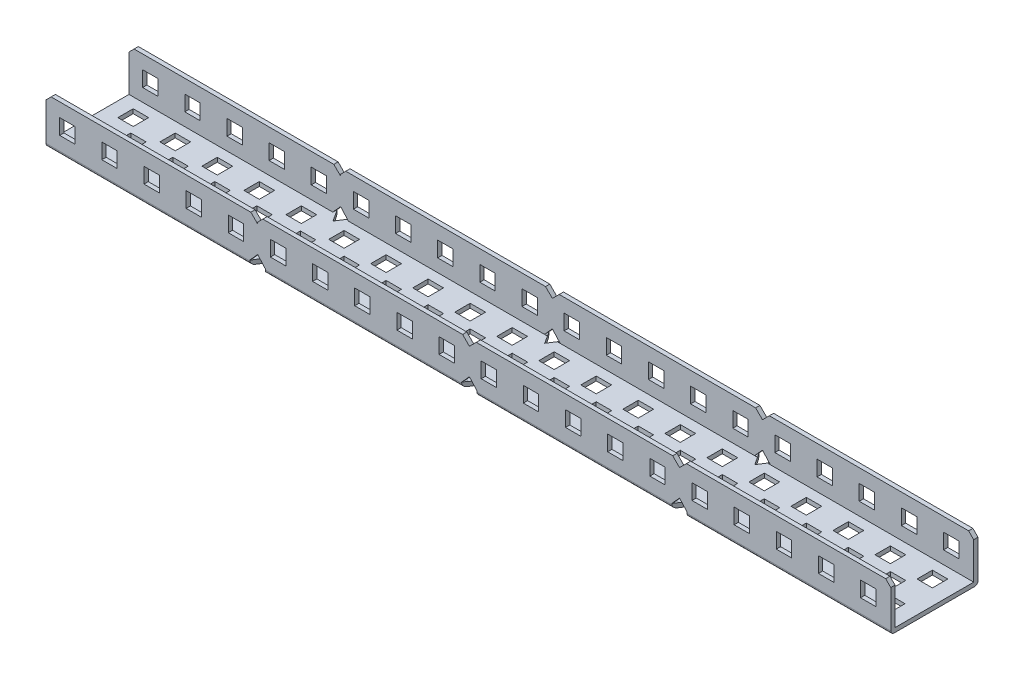
SolidWorks part; units mm, degrees
ref_plane "Front Plane" through (0, 0, 0) normal (0, 0, 1) x (1, 0, 0)
ref_plane "Top Plane" through (0, 0, 0) normal (0, 1, 0) x (1, 0, 0)
ref_plane "Right Plane" through (0, 0, 0) normal (1, 0, 0) x (0, 0, -1)
sketch "Sketch1" plane through (0, 0, 0) normal (0, 1, 0) x (1, 0, 0)
  line L1 (0, 0) -> (191, 0)
  line L2 (0, 0) -> (0, 25.5)
  line L3 (0, 25.5) -> (191, 25.5)
  line L4 (191, 0) -> (191, 25.5)
  dimension "D1" = 25.5
  dimension "D2" = 191
extrude "Boss-Extrude1" add sketch "Sketch1" along normal blind 1.25
sketch "Sketch2" plane through (0, 1.25, 0) normal (0, 1, 0) x (1, 0, 0)
  line L0 (191, 0) -> (191, 25.5) construction
  line L1 (0, 25.5) -> (191, 25.5)
  line L2 (0, 25.5) -> (0, 24.25)
  line L3 (0, 24.25) -> (191, 24.25)
  line L4 (191, 25.5) -> (191, 24.25)
  line L5 (0, 25.5) -> (0, 0) construction
  line L6 (191, 0) -> (0, 0)
  line L7 (191, 0) -> (191, 1.25)
  line L8 (191, 1.25) -> (0, 1.25)
  line L9 (0, 0) -> (0, 1.25)
  dimension "D1" = 1.25
  dimension "D2" = 1.25
extrude "Boss-Extrude2" add sketch "Sketch2" along normal blind 12.25
sketch "Sketch3" plane through (0, 0, 0) normal (0, -1, 0) x (-1, 0, 0)
  line L0 (0, 25.5) -> (0, 0) construction
  line L1 (-4, 4.25) -> (-8.5, 4.25)
  line L2 (-4, 4.25) -> (-4, 8.75)
  line L3 (-4, 8.75) -> (-8.5, 8.75)
  line L4 (-8.5, 4.25) -> (-8.5, 8.75)
  line L5 (-4, 16.75) -> (-8.5, 16.75)
  line L6 (-4, 16.75) -> (-4, 21.25)
  line L7 (-4, 21.25) -> (-8.5, 21.25)
  line L8 (-8.5, 16.75) -> (-8.5, 21.25)
  line L9 (-191, 25.5) -> (0, 25.5) construction
  line L10 (-16.2857, 4.25) -> (-20.7857, 4.25)
  line L11 (-10.5, 10.25) -> (-15, 10.25)
  line L12 (-10.5, 10.25) -> (-10.5, 14.75)
  line L13 (-10.5, 14.75) -> (-15, 14.75)
  line L14 (-15, 10.25) -> (-15, 14.75)
  line L15 (-16.2857, 4.25) -> (-16.2857, 8.75)
  line L16 (-16.2857, 8.75) -> (-20.7857, 8.75)
  line L17 (-20.7857, 4.25) -> (-20.7857, 8.75)
  line L18 (-16.2857, 16.75) -> (-20.7857, 16.75)
  line L19 (-16.2857, 16.75) -> (-16.2857, 21.25)
  line L20 (-16.2857, 21.25) -> (-20.7857, 21.25)
  line L21 (-20.7857, 16.75) -> (-20.7857, 21.25)
  line L22 (-22.7857, 10.25) -> (-27.2857, 10.25)
  line L23 (-22.7857, 10.25) -> (-22.7857, 14.75)
  line L24 (-22.7857, 14.75) -> (-27.2857, 14.75)
  line L25 (-27.2857, 10.25) -> (-27.2857, 14.75)
  line L26 (-28.5714, 4.25) -> (-33.0714, 4.25)
  line L27 (-28.5714, 4.25) -> (-28.5714, 8.75)
  line L28 (-28.5714, 8.75) -> (-33.0714, 8.75)
  line L29 (-33.0714, 4.25) -> (-33.0714, 8.75)
  line L30 (-28.5714, 16.75) -> (-33.0714, 16.75)
  line L31 (-28.5714, 16.75) -> (-28.5714, 21.25)
  line L32 (-28.5714, 21.25) -> (-33.0714, 21.25)
  line L33 (-33.0714, 16.75) -> (-33.0714, 21.25)
  line L34 (-35.0714, 10.25) -> (-39.5714, 10.25)
  line L35 (-35.0714, 10.25) -> (-35.0714, 14.75)
  line L36 (-35.0714, 14.75) -> (-39.5714, 14.75)
  line L37 (-39.5714, 10.25) -> (-39.5714, 14.75)
  line L38 (-40.8571, 4.25) -> (-45.3571, 4.25)
  line L39 (-40.8571, 4.25) -> (-40.8571, 8.75)
  line L40 (-40.8571, 8.75) -> (-45.3571, 8.75)
  line L41 (-45.3571, 4.25) -> (-45.3571, 8.75)
  line L42 (-40.8571, 16.75) -> (-45.3571, 16.75)
  line L43 (-40.8571, 16.75) -> (-40.8571, 21.25)
  line L44 (-40.8571, 21.25) -> (-45.3571, 21.25)
  line L45 (-45.3571, 16.75) -> (-45.3571, 21.25)
  line L46 (-47.3571, 10.25) -> (-51.8571, 10.25)
  line L47 (-47.3571, 10.25) -> (-47.3571, 14.75)
  line L48 (-47.3571, 14.75) -> (-51.8571, 14.75)
  line L49 (-51.8571, 10.25) -> (-51.8571, 14.75)
  line L50 (-53.1429, 4.25) -> (-57.6429, 4.25)
  line L51 (-53.1429, 4.25) -> (-53.1429, 8.75)
  line L52 (-53.1429, 8.75) -> (-57.6429, 8.75)
  line L53 (-57.6429, 4.25) -> (-57.6429, 8.75)
  line L54 (-53.1429, 16.75) -> (-57.6429, 16.75)
  line L55 (-53.1429, 16.75) -> (-53.1429, 21.25)
  line L56 (-53.1429, 21.25) -> (-57.6429, 21.25)
  line L57 (-57.6429, 16.75) -> (-57.6429, 21.25)
  line L58 (-59.6429, 10.25) -> (-64.1429, 10.25)
  line L59 (-59.6429, 10.25) -> (-59.6429, 14.75)
  line L60 (-59.6429, 14.75) -> (-64.1429, 14.75)
  line L61 (-64.1429, 10.25) -> (-64.1429, 14.75)
  line L62 (-65.4286, 4.25) -> (-69.9286, 4.25)
  line L63 (-65.4286, 4.25) -> (-65.4286, 8.75)
  line L64 (-65.4286, 8.75) -> (-69.9286, 8.75)
  line L65 (-69.9286, 4.25) -> (-69.9286, 8.75)
  line L66 (-65.4286, 16.75) -> (-69.9286, 16.75)
  line L67 (-65.4286, 16.75) -> (-65.4286, 21.25)
  line L68 (-65.4286, 21.25) -> (-69.9286, 21.25)
  line L69 (-69.9286, 16.75) -> (-69.9286, 21.25)
  line L70 (-71.9286, 10.25) -> (-76.4286, 10.25)
  line L71 (-71.9286, 10.25) -> (-71.9286, 14.75)
  line L72 (-71.9286, 14.75) -> (-76.4286, 14.75)
  line L73 (-76.4286, 10.25) -> (-76.4286, 14.75)
  line L74 (-77.7143, 4.25) -> (-82.2143, 4.25)
  line L75 (-77.7143, 4.25) -> (-77.7143, 8.75)
  line L76 (-77.7143, 8.75) -> (-82.2143, 8.75)
  line L77 (-82.2143, 4.25) -> (-82.2143, 8.75)
  line L78 (-77.7143, 16.75) -> (-82.2143, 16.75)
  line L79 (-77.7143, 16.75) -> (-77.7143, 21.25)
  line L80 (-77.7143, 21.25) -> (-82.2143, 21.25)
  line L81 (-82.2143, 16.75) -> (-82.2143, 21.25)
  line L82 (-84.2143, 10.25) -> (-88.7143, 10.25)
  line L83 (-84.2143, 10.25) -> (-84.2143, 14.75)
  line L84 (-84.2143, 14.75) -> (-88.7143, 14.75)
  line L85 (-88.7143, 10.25) -> (-88.7143, 14.75)
  line L86 (-90, 4.25) -> (-94.5, 4.25)
  line L87 (-90, 4.25) -> (-90, 8.75)
  line L88 (-90, 8.75) -> (-94.5, 8.75)
  line L89 (-94.5, 4.25) -> (-94.5, 8.75)
  line L90 (-90, 16.75) -> (-94.5, 16.75)
  line L91 (-90, 16.75) -> (-90, 21.25)
  line L92 (-90, 21.25) -> (-94.5, 21.25)
  line L93 (-94.5, 16.75) -> (-94.5, 21.25)
  line L94 (-96.5, 10.25) -> (-101, 10.25)
  line L95 (-96.5, 10.25) -> (-96.5, 14.75)
  line L96 (-96.5, 14.75) -> (-101, 14.75)
  line L97 (-101, 10.25) -> (-101, 14.75)
  line L98 (-102.2857, 4.25) -> (-106.7857, 4.25)
  line L99 (-102.2857, 4.25) -> (-102.2857, 8.75)
  line L100 (-102.2857, 8.75) -> (-106.7857, 8.75)
  line L101 (-106.7857, 4.25) -> (-106.7857, 8.75)
  line L102 (-102.2857, 16.75) -> (-106.7857, 16.75)
  line L103 (-102.2857, 16.75) -> (-102.2857, 21.25)
  line L104 (-102.2857, 21.25) -> (-106.7857, 21.25)
  line L105 (-106.7857, 16.75) -> (-106.7857, 21.25)
  line L106 (-108.7857, 10.25) -> (-113.2857, 10.25)
  line L107 (-108.7857, 10.25) -> (-108.7857, 14.75)
  line L108 (-108.7857, 14.75) -> (-113.2857, 14.75)
  line L109 (-113.2857, 10.25) -> (-113.2857, 14.75)
  line L110 (-114.5714, 4.25) -> (-119.0714, 4.25)
  line L111 (-114.5714, 4.25) -> (-114.5714, 8.75)
  line L112 (-114.5714, 8.75) -> (-119.0714, 8.75)
  line L113 (-119.0714, 4.25) -> (-119.0714, 8.75)
  line L114 (-114.5714, 16.75) -> (-119.0714, 16.75)
  line L115 (-114.5714, 16.75) -> (-114.5714, 21.25)
  line L116 (-114.5714, 21.25) -> (-119.0714, 21.25)
  line L117 (-119.0714, 16.75) -> (-119.0714, 21.25)
  line L118 (-121.0714, 10.25) -> (-125.5714, 10.25)
  line L119 (-121.0714, 10.25) -> (-121.0714, 14.75)
  line L120 (-121.0714, 14.75) -> (-125.5714, 14.75)
  line L121 (-125.5714, 10.25) -> (-125.5714, 14.75)
  line L122 (-126.8571, 4.25) -> (-131.3571, 4.25)
  line L123 (-126.8571, 4.25) -> (-126.8571, 8.75)
  line L124 (-126.8571, 8.75) -> (-131.3571, 8.75)
  line L125 (-131.3571, 4.25) -> (-131.3571, 8.75)
  line L126 (-126.8571, 16.75) -> (-131.3571, 16.75)
  line L127 (-126.8571, 16.75) -> (-126.8571, 21.25)
  line L128 (-126.8571, 21.25) -> (-131.3571, 21.25)
  line L129 (-131.3571, 16.75) -> (-131.3571, 21.25)
  line L130 (-133.3571, 10.25) -> (-137.8571, 10.25)
  line L131 (-133.3571, 10.25) -> (-133.3571, 14.75)
  line L132 (-133.3571, 14.75) -> (-137.8571, 14.75)
  line L133 (-137.8571, 10.25) -> (-137.8571, 14.75)
  line L134 (-139.1429, 4.25) -> (-143.6429, 4.25)
  line L135 (-139.1429, 4.25) -> (-139.1429, 8.75)
  line L136 (-139.1429, 8.75) -> (-143.6429, 8.75)
  line L137 (-143.6429, 4.25) -> (-143.6429, 8.75)
  line L138 (-139.1429, 16.75) -> (-143.6429, 16.75)
  line L139 (-139.1429, 16.75) -> (-139.1429, 21.25)
  line L140 (-139.1429, 21.25) -> (-143.6429, 21.25)
  line L141 (-143.6429, 16.75) -> (-143.6429, 21.25)
  line L142 (-145.6429, 10.25) -> (-150.1429, 10.25)
  line L143 (-145.6429, 10.25) -> (-145.6429, 14.75)
  line L144 (-145.6429, 14.75) -> (-150.1429, 14.75)
  line L145 (-150.1429, 10.25) -> (-150.1429, 14.75)
  line L146 (-151.4286, 4.25) -> (-155.9286, 4.25)
  line L147 (-151.4286, 4.25) -> (-151.4286, 8.75)
  line L148 (-151.4286, 8.75) -> (-155.9286, 8.75)
  line L149 (-155.9286, 4.25) -> (-155.9286, 8.75)
  line L150 (-151.4286, 16.75) -> (-155.9286, 16.75)
  line L151 (-151.4286, 16.75) -> (-151.4286, 21.25)
  line L152 (-151.4286, 21.25) -> (-155.9286, 21.25)
  line L153 (-155.9286, 16.75) -> (-155.9286, 21.25)
  line L154 (-157.9286, 10.25) -> (-162.4286, 10.25)
  line L155 (-157.9286, 10.25) -> (-157.9286, 14.75)
  line L156 (-157.9286, 14.75) -> (-162.4286, 14.75)
  line L157 (-162.4286, 10.25) -> (-162.4286, 14.75)
  line L158 (-163.7143, 4.25) -> (-168.2143, 4.25)
  line L159 (-163.7143, 4.25) -> (-163.7143, 8.75)
  line L160 (-163.7143, 8.75) -> (-168.2143, 8.75)
  line L161 (-168.2143, 4.25) -> (-168.2143, 8.75)
  line L162 (-163.7143, 16.75) -> (-168.2143, 16.75)
  line L163 (-163.7143, 16.75) -> (-163.7143, 21.25)
  line L164 (-163.7143, 21.25) -> (-168.2143, 21.25)
  line L165 (-168.2143, 16.75) -> (-168.2143, 21.25)
  line L166 (-170.2143, 10.25) -> (-174.7143, 10.25)
  line L167 (-170.2143, 10.25) -> (-170.2143, 14.75)
  line L168 (-170.2143, 14.75) -> (-174.7143, 14.75)
  line L169 (-174.7143, 10.25) -> (-174.7143, 14.75)
  line L170 (-176, 4.25) -> (-180.5, 4.25)
  line L171 (-176, 4.25) -> (-176, 8.75)
  line L172 (-176, 8.75) -> (-180.5, 8.75)
  line L173 (-180.5, 4.25) -> (-180.5, 8.75)
  line L174 (-176, 16.75) -> (-180.5, 16.75)
  line L175 (-176, 16.75) -> (-176, 21.25)
  line L176 (-176, 21.25) -> (-180.5, 21.25)
  line L177 (-180.5, 16.75) -> (-180.5, 21.25)
  line L178 (-182.5, 10.25) -> (-187, 10.25)
  line L179 (-182.5, 10.25) -> (-182.5, 14.75)
  line L180 (-182.5, 14.75) -> (-187, 14.75)
  line L181 (-187, 10.25) -> (-187, 14.75)
  line L182 (-191, 0) -> (-191, 25.5) construction
  dimension "D1" = 4.5
  dimension "D2" = 4
  dimension "D3" = 8
  dimension "D4" = 4.25
  dimension "D5" = 2
  dimension "D6" = 2
  dimension "D8" = 4
  dimension "D7" = 15
extrude "Cut-Extrude1" cut sketch "Sketch3" against normal blind 12.25
sketch "Sketch4" plane through (0, 0, 0) normal (0, -1, 0) x (1, 0, 0)
  line L0 (61.8929, -3.5) -> (59.6429, 0)
  line L1 (0, 0) -> (191, 0) construction
  line L2 (61.8929, -3.5) -> (64.1429, 0)
  line L3 (59.6429, 0) -> (64.1429, 0)
  line L4 (64.1429, -10.25) -> (59.6429, -10.25) construction
  line L6 (123.3214, -3.5) -> (121.0714, 0)
  line L7 (121.0714, 0) -> (125.5714, 0)
  line L8 (123.3214, -3.5) -> (125.5714, 0)
  line L9 (125.5714, -10.25) -> (121.0714, -10.25) construction
  line L10 (0, -12.75) -> (219.3109, -12.75) construction
  line L12 (121.0714, -25.5) -> (125.5714, -25.5)
  line L13 (123.3214, -22) -> (125.5714, -25.5)
  line L14 (123.3214, -22) -> (121.0714, -25.5)
  line L15 (59.6429, -25.5) -> (64.1429, -25.5)
  line L16 (61.8929, -22) -> (59.6429, -25.5)
  line L17 (61.8929, -22) -> (64.1429, -25.5)
  line L18 (4, -16.75) -> (4, -21.25) construction
  line L19 (47.3571, -14.75) -> (51.8571, -14.75) construction
  point P0 (61.8929, 0)
  point P8 (61.8929, -10.25)
  point P15 (123.3214, -10.25)
  dimension "D1" = 4.5
  dimension "D2" = 3.5
  dimension "D3" = 2
  dimension "D4" = 47.8571
  dimension "D5" = 2
  dimension "D6" = 7.25
extrude "Cut-Extrude2" cut sketch "Sketch4" against normal blind 1.3
sketch "Sketch6" plane through (0, 0, -25.5) normal (0, 0, -1) x (-1, 0, 0)
  line L0 (-125.5714, 1.3) -> (-123.3214, 3.8)
  line L1 (-123.3214, 3.8) -> (-121.0714, 1.3)
  line L2 (-125.5714, 0) -> (-121.0714, 0)
  line L3 (-125.5714, 1.3) -> (-121.0714, 1.3)
  line L4 (-64.1429, 1.3) -> (-61.8929, 3.8)
  line L5 (-61.8929, 3.8) -> (-59.6429, 1.3)
  line L6 (-64.1429, 1.3) -> (-59.6429, 1.3)
  line L8 (-125.3214, 13.5) -> (-121.3214, 13.5)
  line L9 (-125.3214, 13.5) -> (-123.3214, 11.5)
  line L10 (-191, 13.5) -> (0, 13.5) construction
  line L11 (-123.3214, 11.5) -> (-121.3214, 13.5)
  line L12 (-63.8929, 13.5) -> (-61.8929, 11.5)
  line L13 (-61.8929, 11.5) -> (-59.8929, 13.5)
  line L14 (-63.8929, 13.5) -> (-59.8929, 13.5)
  point P29 (-123.3214, 13.5)
  point P31 (-61.8929, 13.5)
  line M2 (-125.5714, 1.3) -> (-121.0714, 1.3)
  line M6 (-64.1429, 1.3) -> (-59.6429, 1.3)
  dimension "D1" = 2.5
  dimension "D3" = 4
  dimension "D4" = 4
  dimension "D5" = 2
  dimension "D2" = 2
extrude "Cut-Extrude4" cut sketch "Sketch6" against normal blind 48.3 contours L1 L0 M2 | L5 L4 M6 | L8 L11 L9 | L14 L13 L12
sketch "Sketch7" plane through (0, 0, -25.5) normal (0, 0, -1) x (-1, 0, 0)
  line L0 (-191, 13.5) -> (-191, 12)
  line L1 (-191, 13.5) -> (-191, 0) construction
  line L2 (-191, 12) -> (-189.5, 13.5)
  line L3 (-191, 13.5) -> (-125.3214, 13.5) construction
  line L4 (-189.5, 13.5) -> (-191, 13.5)
  line L5 (-1.5, 13.5) -> (0, 13.5)
  line L6 (-59.8929, 13.5) -> (0, 13.5) construction
  line L7 (0, 13.5) -> (0, 12)
  line L8 (0, 13.5) -> (0, 0) construction
  line L9 (0, 12) -> (-1.5, 13.5)
  dimension "D1" = 1.5
  dimension "D2" = 1.5
  dimension "D3" = 1.5
  dimension "D4" = 1.5
extrude "Cut-Extrude5" cut sketch "Sketch7" against normal blind 48.3
fillet "Fillet1" radius 1 6 edges at (158.2857, 0, 0) (92.6071, 0, 0) (29.8214, 0, 0) (29.8214, 0, -25.5) (92.6071, 0, -25.5) (158.2857, 0, -25.5)
sketch "Sketch8" plane through (0, 0, 0) normal (0, -1, 0) x (1, 0, 0)
  line L0 (61.8929, -22) -> (59.6429, -25.5)
  line L1 (61.8929, -25.5) -> (0, -25.5)
  line L2 (61.8929, -25.5) -> (61.8929, 0)
  line L3 (61.8929, 0) -> (0, 0)
  line L4 (0, -25.5) -> (0, 0)
  line L5 (57.6429, -21.25) -> (53.1429, -21.25)
  line L6 (57.6429, -21.25) -> (57.6429, -16.75)
  line L7 (57.6429, -16.75) -> (53.1429, -16.75)
  line L8 (53.1429, -21.25) -> (53.1429, -16.75)
  line L9 (51.8571, -14.75) -> (47.3571, -14.75)
  line L10 (51.8571, -14.75) -> (51.8571, -10.25)
  line L11 (51.8571, -10.25) -> (47.3571, -10.25)
  line L12 (47.3571, -14.75) -> (47.3571, -10.25)
  line L13 (45.3571, -21.25) -> (40.8571, -21.25)
  line L14 (45.3571, -21.25) -> (45.3571, -16.75)
  line L15 (45.3571, -16.75) -> (40.8571, -16.75)
  line L16 (40.8571, -21.25) -> (40.8571, -16.75)
  line L17 (45.3571, -8.75) -> (40.8571, -8.75)
  line L18 (45.3571, -8.75) -> (45.3571, -4.25)
  line L19 (45.3571, -4.25) -> (40.8571, -4.25)
  line L20 (40.8571, -8.75) -> (40.8571, -4.25)
  line L21 (57.6429, -8.75) -> (53.1429, -8.75)
  line L22 (57.6429, -8.75) -> (57.6429, -4.25)
  line L23 (57.6429, -4.25) -> (53.1429, -4.25)
  line L24 (53.1429, -8.75) -> (53.1429, -4.25)
  line L25 (39.5714, -14.75) -> (35.0714, -14.75)
  line L26 (39.5714, -14.75) -> (39.5714, -10.25)
  line L27 (39.5714, -10.25) -> (35.0714, -10.25)
  line L28 (35.0714, -14.75) -> (35.0714, -10.25)
  line L29 (33.0714, -21.25) -> (28.5714, -21.25)
  line L30 (33.0714, -21.25) -> (33.0714, -16.75)
  line L31 (33.0714, -16.75) -> (28.5714, -16.75)
  line L32 (28.5714, -21.25) -> (28.5714, -16.75)
  line L33 (33.0714, -8.75) -> (28.5714, -8.75)
  line L34 (33.0714, -8.75) -> (33.0714, -4.25)
  line L35 (33.0714, -4.25) -> (28.5714, -4.25)
  line L36 (28.5714, -8.75) -> (28.5714, -4.25)
  line L37 (27.2857, -14.75) -> (22.7857, -14.75)
  line L38 (27.2857, -14.75) -> (27.2857, -10.25)
  line L39 (27.2857, -10.25) -> (22.7857, -10.25)
  line L40 (22.7857, -14.75) -> (22.7857, -10.25)
  line L41 (20.7857, -21.25) -> (16.2857, -21.25)
  line L42 (20.7857, -21.25) -> (20.7857, -16.75)
  line L43 (20.7857, -16.75) -> (16.2857, -16.75)
  line L44 (16.2857, -21.25) -> (16.2857, -16.75)
  line L45 (20.7857, -8.75) -> (16.2857, -8.75)
  line L46 (20.7857, -8.75) -> (20.7857, -4.25)
  line L47 (20.7857, -4.25) -> (16.2857, -4.25)
  line L48 (16.2857, -8.75) -> (16.2857, -4.25)
  line L49 (15, -14.75) -> (10.5, -14.75)
  line L50 (15, -14.75) -> (15, -10.25)
  line L51 (15, -10.25) -> (10.5, -10.25)
  line L52 (10.5, -14.75) -> (10.5, -10.25)
  line L53 (8.5, -21.25) -> (4, -21.25)
  line L54 (8.5, -21.25) -> (8.5, -16.75)
  line L55 (8.5, -16.75) -> (4, -16.75)
  line L56 (4, -21.25) -> (4, -16.75)
  line L57 (8.5, -8.75) -> (4, -8.75)
  line L58 (8.5, -8.75) -> (8.5, -4.25)
  line L59 (8.5, -4.25) -> (4, -4.25)
  line L60 (4, -8.75) -> (4, -4.25)
  line L61 (59.6429, -25.5) -> (61.8929, -25.5)
  line L62 (61.8929, -3.5) -> (59.6429, 0)
  line L63 (59.6429, 0) -> (61.8929, 0)
  line L64 (0, -22) -> (-2.25, -25.5)
  line L65 (0, -25.5) -> (-61.8929, -25.5)
  line L66 (0, -25.5) -> (0, 0)
  line L67 (0, 0) -> (-61.8929, 0)
  line L68 (-61.8929, -25.5) -> (-61.8929, 0)
  line L69 (-4.25, -21.25) -> (-8.75, -21.25)
  line L70 (-4.25, -21.25) -> (-4.25, -16.75)
  line L71 (-4.25, -16.75) -> (-8.75, -16.75)
  line L72 (-8.75, -21.25) -> (-8.75, -16.75)
  line L73 (-10.0357, -14.75) -> (-14.5357, -14.75)
  line L74 (-10.0357, -14.75) -> (-10.0357, -10.25)
  line L75 (-10.0357, -10.25) -> (-14.5357, -10.25)
  line L76 (-14.5357, -14.75) -> (-14.5357, -10.25)
  line L77 (-16.5357, -21.25) -> (-21.0357, -21.25)
  line L78 (-16.5357, -21.25) -> (-16.5357, -16.75)
  line L79 (-16.5357, -16.75) -> (-21.0357, -16.75)
  line L80 (-21.0357, -21.25) -> (-21.0357, -16.75)
  line L81 (-16.5357, -8.75) -> (-21.0357, -8.75)
  line L82 (-16.5357, -8.75) -> (-16.5357, -4.25)
  line L83 (-16.5357, -4.25) -> (-21.0357, -4.25)
  line L84 (-21.0357, -8.75) -> (-21.0357, -4.25)
  line L85 (-4.25, -8.75) -> (-8.75, -8.75)
  line L86 (-4.25, -8.75) -> (-4.25, -4.25)
  line L87 (-4.25, -4.25) -> (-8.75, -4.25)
  line L88 (-8.75, -8.75) -> (-8.75, -4.25)
  line L89 (-22.3214, -14.75) -> (-26.8214, -14.75)
  line L90 (-22.3214, -14.75) -> (-22.3214, -10.25)
  line L91 (-22.3214, -10.25) -> (-26.8214, -10.25)
  line L92 (-26.8214, -14.75) -> (-26.8214, -10.25)
  line L93 (-28.8214, -21.25) -> (-33.3214, -21.25)
  line L94 (-28.8214, -21.25) -> (-28.8214, -16.75)
  line L95 (-28.8214, -16.75) -> (-33.3214, -16.75)
  line L96 (-33.3214, -21.25) -> (-33.3214, -16.75)
  line L97 (-28.8214, -8.75) -> (-33.3214, -8.75)
  line L98 (-28.8214, -8.75) -> (-28.8214, -4.25)
  line L99 (-28.8214, -4.25) -> (-33.3214, -4.25)
  line L100 (-33.3214, -8.75) -> (-33.3214, -4.25)
  line L101 (-34.6071, -14.75) -> (-39.1071, -14.75)
  line L102 (-34.6071, -14.75) -> (-34.6071, -10.25)
  line L103 (-34.6071, -10.25) -> (-39.1071, -10.25)
  line L104 (-39.1071, -14.75) -> (-39.1071, -10.25)
  line L105 (-41.1071, -21.25) -> (-45.6071, -21.25)
  line L106 (-41.1071, -21.25) -> (-41.1071, -16.75)
  line L107 (-41.1071, -16.75) -> (-45.6071, -16.75)
  line L108 (-45.6071, -21.25) -> (-45.6071, -16.75)
  line L109 (-41.1071, -8.75) -> (-45.6071, -8.75)
  line L110 (-41.1071, -8.75) -> (-41.1071, -4.25)
  line L111 (-41.1071, -4.25) -> (-45.6071, -4.25)
  line L112 (-45.6071, -8.75) -> (-45.6071, -4.25)
  line L113 (-46.8929, -14.75) -> (-51.3929, -14.75)
  line L114 (-46.8929, -14.75) -> (-46.8929, -10.25)
  line L115 (-46.8929, -10.25) -> (-51.3929, -10.25)
  line L116 (-51.3929, -14.75) -> (-51.3929, -10.25)
  line L117 (-53.3929, -21.25) -> (-57.8929, -21.25)
  line L118 (-53.3929, -21.25) -> (-53.3929, -16.75)
  line L119 (-53.3929, -16.75) -> (-57.8929, -16.75)
  line L120 (-57.8929, -21.25) -> (-57.8929, -16.75)
  line L121 (-53.3929, -8.75) -> (-57.8929, -8.75)
  line L122 (-53.3929, -8.75) -> (-53.3929, -4.25)
  line L123 (-53.3929, -4.25) -> (-57.8929, -4.25)
  line L124 (-57.8929, -8.75) -> (-57.8929, -4.25)
  line L125 (-2.25, -25.5) -> (0, -25.5)
  line L126 (0, -3.5) -> (-2.25, 0)
  line L127 (-2.25, 0) -> (0, 0)
  line L128 (0, -3.5) -> (2.25, 0)
  line L129 (2.25, -14.75) -> (-2.25, -14.75)
  line L130 (2.25, -14.75) -> (2.25, -10.25)
  line L131 (2.25, -10.25) -> (-2.25, -10.25)
  line L132 (-2.25, -14.75) -> (-2.25, -10.25)
  line L133 (0, -22) -> (2.25, -25.5)
  point P175 (0, -10.25)
  dimension "D2" = 4.5
  dimension "D1" = 2
extrude "Boss-Extrude3" add sketch "Sketch8" against normal blind 1.25 contours L129 L132 L131 L4 L126 L67 L68 L65 L64 L69 L72 L71 L70 L73 L76 L75 L74 L77 L80 L79 L78 L81 L84 L83 L82 L85 L88 L87 L86 L89 L92 L91 L90 L93 L96 L95 L94 L97 L100 L99 L98
sketch "Sketch9" plane through (0, 0, 0) normal (0, -1, 0) x (1, 0, 0)
  line L0 (0, -22) -> (-2.25, -25.5)
  line L1 (-2.25, -25.5) -> (2.25, -25.5)
  line L2 (0, -25.5) -> (0, -22)
  line L3 (-2.25, 0) -> (0, -3.5)
  line L4 (0, -3.5) -> (0, 0)
  line L5 (2.25, 0) -> (-2.25, 0)
  line L6 (0, -22) -> (2.25, -25.5)
  line L7 (2.25, 0) -> (0, -3.5)
  line L8 (2.25, -10.25) -> (-2.25, -10.25)
  line L9 (-2.25, -10.25) -> (-2.25, -14.75)
  line L10 (-2.25, -14.75) -> (2.25, -14.75)
  line L11 (0, -14.75) -> (0, -10.25)
  line L12 (2.25, -10.25) -> (2.25, -14.75)
extrude "Cut-Extrude6" cut sketch "Sketch9" against normal blind 1.25 contours L12 L8 L11 L10 | L6 L2 L1 | L3 L5 L7
sketch "Sketch10" plane through (0, 0, 0) normal (0, 0, 1) x (1, 0, 0)
  line L0 (1.5, 13.5) -> (0, 12)
  line L1 (0, 12) -> (0, 1.25)
  line L2 (1.5, 13.5) -> (59.8929, 13.5)
  line L3 (59.8929, 13.5) -> (61.8929, 11.5)
  line L4 (61.8929, 11.5) -> (61.8929, 3.8)
  line L5 (61.8929, 3.8) -> (59.6429, 1.3)
  line L6 (59.6429, 1.3) -> (59.6429, 1)
  line L7 (0, 1.25) -> (0, 0)
  line L8 (0, 0) -> (61.8929, 0)
  line L9 (61.8929, 0) -> (61.8929, 3.8)
  line L10 (30.6964, 13.5) -> (30.6964, -8.0722) construction
  line L11 (0, 1.25) -> (2.25, 1.25)
  line L12 (-60.3929, 13.5) -> (-61.8929, 12)
  line L13 (-61.8929, 12) -> (-61.8929, 1.25)
  line L14 (-60.3929, 13.5) -> (-2, 13.5)
  line L15 (-2, 13.5) -> (0, 11.5)
  line L16 (0, 11.5) -> (0, 3.8)
  line L17 (0, 3.8) -> (-2.25, 1.3)
  line L18 (0, 3.8) -> (2.25, 1.25)
  line L19 (-61.8929, 1.25) -> (-61.8929, 0)
  line L20 (-61.8929, 0) -> (0, 0)
  line L21 (0, 0) -> (0, 3.8)
  line L22 (-61.8929, 1.25) -> (-59.6429, 1.25)
  line L23 (-31.1964, 13.5) -> (-31.1964, -8.0722) construction
  line L24 (0, 11.5) -> (2, 13.5)
  line L25 (2, 13.5) -> (-2, 13.5)
  line L26 (-2.25, 1.3) -> (-2.25, 0)
  line L28 (-2.25, 1.3) -> (-2.25, 1) [skipped]
  spline S0 degree 2 poles (59.6429, 1) (59.6889, 0.0907) (60.2857, 0) knots 0 0 0 1 1 1
  dimension "D2" = 4
  dimension "D1" = 2
extrude "Boss-Extrude4" add sketch "Sketch10" against normal blind 25.5
sketch "Sketch11" plane through (191, 0, 0) normal (1, 0, 0) x (0, 0, -1)
  line L0 (1.25, 13.5) -> (1.25, 1.25)
  line L1 (1.25, 1.25) -> (24.25, 1.25)
  line L2 (24.25, 1.25) -> (24.25, 13.5)
  line L3 (24.25, 13.5) -> (1.25, 13.5)
extrude "Cut-Extrude7" cut sketch "Sketch11" against normal blind 284.5
sketch "Sketch12" plane through (0, 0, 0) normal (0, -1, 0) x (1, 0, 0)
  line L0 (0, 0) -> (0, -30.8239) construction
  line L1 (57.6429, -4.25) -> (53.1429, -4.25)
  line L2 (57.6429, -4.25) -> (57.6429, -8.75)
  line L3 (57.6429, -8.75) -> (53.1429, -8.75)
  line L4 (53.1429, -4.25) -> (53.1429, -8.75)
  line L5 (51.8571, -10.25) -> (47.3571, -10.25)
  line L6 (51.8571, -10.25) -> (51.8571, -14.75)
  line L7 (51.8571, -14.75) -> (47.3571, -14.75)
  line L8 (47.3571, -10.25) -> (47.3571, -14.75)
  line L9 (45.3571, -16.75) -> (40.8571, -16.75)
  line L10 (45.3571, -16.75) -> (45.3571, -21.25)
  line L11 (45.3571, -21.25) -> (40.8571, -21.25)
  line L12 (40.8571, -16.75) -> (40.8571, -21.25)
  line L13 (53.1429, -16.75) -> (57.6429, -16.75)
  line L14 (53.1429, -16.75) -> (53.1429, -21.25)
  line L15 (53.1429, -21.25) -> (57.6429, -21.25)
  line L16 (57.6429, -16.75) -> (57.6429, -21.25)
  line L17 (45.3571, -4.25) -> (40.8571, -4.25)
  line L18 (45.3571, -4.25) -> (45.3571, -8.75)
  line L19 (45.3571, -8.75) -> (40.8571, -8.75)
  line L20 (40.8571, -4.25) -> (40.8571, -8.75)
  line L21 (39.5714, -10.25) -> (35.0714, -10.25)
  line L22 (39.5714, -10.25) -> (39.5714, -14.75)
  line L23 (39.5714, -14.75) -> (35.0714, -14.75)
  line L24 (35.0714, -10.25) -> (35.0714, -14.75)
  line L25 (33.0714, -4.25) -> (28.5714, -4.25)
  line L26 (33.0714, -4.25) -> (33.0714, -8.75)
  line L27 (33.0714, -8.75) -> (28.5714, -8.75)
  line L28 (28.5714, -4.25) -> (28.5714, -8.75)
  line L29 (33.0714, -16.75) -> (28.5714, -16.75)
  line L30 (33.0714, -16.75) -> (33.0714, -21.25)
  line L31 (33.0714, -21.25) -> (28.5714, -21.25)
  line L32 (28.5714, -16.75) -> (28.5714, -21.25)
  line L33 (27.2857, -10.25) -> (22.7857, -10.25)
  line L34 (27.2857, -10.25) -> (27.2857, -14.75)
  line L35 (27.2857, -14.75) -> (22.7857, -14.75)
  line L36 (22.7857, -10.25) -> (22.7857, -14.75)
  line L37 (20.7857, -4.25) -> (16.2857, -4.25)
  line L38 (20.7857, -4.25) -> (20.7857, -8.75)
  line L39 (20.7857, -8.75) -> (16.2857, -8.75)
  line L40 (16.2857, -4.25) -> (16.2857, -8.75)
  line L41 (20.7857, -16.75) -> (16.2857, -16.75)
  line L42 (20.7857, -16.75) -> (20.7857, -21.25)
  line L43 (20.7857, -21.25) -> (16.2857, -21.25)
  line L44 (16.2857, -16.75) -> (16.2857, -21.25)
  line L45 (15, -10.25) -> (10.5, -10.25)
  line L46 (15, -10.25) -> (15, -14.75)
  line L47 (15, -14.75) -> (10.5, -14.75)
  line L48 (10.5, -10.25) -> (10.5, -14.75)
  line L49 (8.5, -4.25) -> (4, -4.25)
  line L50 (8.5, -4.25) -> (8.5, -8.75)
  line L51 (8.5, -8.75) -> (4, -8.75)
  line L52 (4, -4.25) -> (4, -8.75)
  line L53 (4, -16.75) -> (8.5, -16.75)
  line L54 (4, -16.75) -> (4, -21.25)
  line L55 (4, -21.25) -> (8.5, -21.25)
  line L56 (8.5, -16.75) -> (8.5, -21.25)
  line L57 (-8.5, -16.75) -> (-8.5, -21.25)
  line L58 (-4, -21.25) -> (-8.5, -21.25)
  line L59 (-4, -16.75) -> (-4, -21.25)
  line L60 (-4, -16.75) -> (-8.5, -16.75)
  line L61 (-4, -4.25) -> (-4, -8.75)
  line L62 (-8.5, -8.75) -> (-4, -8.75)
  line L63 (-8.5, -4.25) -> (-8.5, -8.75)
  line L64 (-8.5, -4.25) -> (-4, -4.25)
  line L65 (-10.5, -10.25) -> (-10.5, -14.75)
  line L66 (-15, -14.75) -> (-10.5, -14.75)
  line L67 (-15, -10.25) -> (-15, -14.75)
  line L68 (-15, -10.25) -> (-10.5, -10.25)
  line L69 (-16.2857, -16.75) -> (-16.2857, -21.25)
  line L70 (-20.7857, -21.25) -> (-16.2857, -21.25)
  line L71 (-20.7857, -16.75) -> (-20.7857, -21.25)
  line L72 (-20.7857, -16.75) -> (-16.2857, -16.75)
  line L73 (-16.2857, -4.25) -> (-16.2857, -8.75)
  line L74 (-20.7857, -8.75) -> (-16.2857, -8.75)
  line L75 (-20.7857, -4.25) -> (-20.7857, -8.75)
  line L76 (-20.7857, -4.25) -> (-16.2857, -4.25)
  line L77 (-22.7857, -10.25) -> (-22.7857, -14.75)
  line L78 (-27.2857, -14.75) -> (-22.7857, -14.75)
  line L79 (-27.2857, -10.25) -> (-27.2857, -14.75)
  line L80 (-27.2857, -10.25) -> (-22.7857, -10.25)
  line L81 (-28.5714, -16.75) -> (-28.5714, -21.25)
  line L82 (-33.0714, -21.25) -> (-28.5714, -21.25)
  line L83 (-33.0714, -16.75) -> (-33.0714, -21.25)
  line L84 (-33.0714, -16.75) -> (-28.5714, -16.75)
  line L85 (-28.5714, -4.25) -> (-28.5714, -8.75)
  line L86 (-33.0714, -8.75) -> (-28.5714, -8.75)
  line L87 (-33.0714, -4.25) -> (-33.0714, -8.75)
  line L88 (-33.0714, -4.25) -> (-28.5714, -4.25)
  line L89 (-35.0714, -10.25) -> (-35.0714, -14.75)
  line L90 (-39.5714, -14.75) -> (-35.0714, -14.75)
  line L91 (-39.5714, -10.25) -> (-39.5714, -14.75)
  line L92 (-39.5714, -10.25) -> (-35.0714, -10.25)
  line L93 (-40.8571, -4.25) -> (-40.8571, -8.75)
  line L94 (-45.3571, -8.75) -> (-40.8571, -8.75)
  line L95 (-45.3571, -4.25) -> (-45.3571, -8.75)
  line L96 (-45.3571, -4.25) -> (-40.8571, -4.25)
  line L97 (-57.6429, -16.75) -> (-57.6429, -21.25)
  line L98 (-53.1429, -21.25) -> (-57.6429, -21.25)
  line L99 (-53.1429, -16.75) -> (-53.1429, -21.25)
  line L100 (-53.1429, -16.75) -> (-57.6429, -16.75)
  line L101 (-40.8571, -16.75) -> (-40.8571, -21.25)
  line L102 (-45.3571, -21.25) -> (-40.8571, -21.25)
  line L103 (-45.3571, -16.75) -> (-45.3571, -21.25)
  line L104 (-45.3571, -16.75) -> (-40.8571, -16.75)
  line L105 (-47.3571, -10.25) -> (-47.3571, -14.75)
  line L106 (-51.8571, -14.75) -> (-47.3571, -14.75)
  line L107 (-51.8571, -10.25) -> (-51.8571, -14.75)
  line L108 (-51.8571, -10.25) -> (-47.3571, -10.25)
  line L109 (-53.1429, -4.25) -> (-53.1429, -8.75)
  line L110 (-57.6429, -8.75) -> (-53.1429, -8.75)
  line L111 (-57.6429, -4.25) -> (-57.6429, -8.75)
  line L112 (-57.6429, -4.25) -> (-53.1429, -4.25)
  point P86 (0, 0)
  point P143 (0, 0)
  point P144 (0, 0)
  point P146 (0, 0)
extrude "Cut-Extrude8" cut sketch "Sketch12" against normal blind 284.5
sketch "Sketch13" plane through (0, 0, -25.5) normal (0, 0, -1) x (-1, 0, 0)
  line L0 (0, 3.8) -> (-2.25, 1.25)
  line L1 (0, 3.8) -> (0, 1.25)
  line L2 (0, 1.25) -> (-2.25, 1.25)
extrude "Cut-Extrude9" cut sketch "Sketch13" against normal blind 284.5
fillet "Fillet2" radius 1 2 edges at (-32.0714, 0, -25.5) (-32.0714, 0, 0)
sketch "Sketch14" plane through (0, 0, 0) normal (0, 0, 1) x (1, 0, 0)
  line L0 (-61.8929, 12) -> (-61.8929, 1) construction
  line L1 (-57.8929, 9.5) -> (-53.3929, 9.5)
  line L2 (-57.8929, 9.5) -> (-57.8929, 5)
  line L3 (-57.8929, 5) -> (-53.3929, 5)
  line L4 (-53.3929, 9.5) -> (-53.3929, 5)
  line L5 (-60.3929, 13.5) -> (-2, 13.5) construction
  line L6 (-45.5696, 9.5) -> (-41.0696, 9.5)
  line L7 (-45.5696, 9.5) -> (-45.5696, 5)
  line L8 (-45.5696, 5) -> (-41.0696, 5)
  line L9 (-41.0696, 9.5) -> (-41.0696, 5)
  line L10 (-33.2464, 9.5) -> (-28.7464, 9.5)
  line L11 (-33.2464, 9.5) -> (-33.2464, 5)
  line L12 (-33.2464, 5) -> (-28.7464, 5)
  line L13 (-28.7464, 9.5) -> (-28.7464, 5)
  line L14 (-20.9232, 9.5) -> (-16.4232, 9.5)
  line L15 (-20.9232, 9.5) -> (-20.9232, 5)
  line L16 (-20.9232, 5) -> (-16.4232, 5)
  line L17 (-16.4232, 9.5) -> (-16.4232, 5)
  line L18 (-8.6, 9.5) -> (-4.1, 9.5)
  line L19 (-8.6, 9.5) -> (-8.6, 5)
  line L20 (-8.6, 5) -> (-4.1, 5)
  line L21 (-4.1, 9.5) -> (-4.1, 5)
  line L22 (3.7232, 9.5) -> (8.2232, 9.5)
  line L23 (3.7232, 9.5) -> (3.7232, 5)
  line L24 (3.7232, 5) -> (8.2232, 5)
  line L25 (8.2232, 9.5) -> (8.2232, 5)
  line L26 (16.0464, 9.5) -> (20.5464, 9.5)
  line L27 (16.0464, 9.5) -> (16.0464, 5)
  line L28 (16.0464, 5) -> (20.5464, 5)
  line L29 (20.5464, 9.5) -> (20.5464, 5)
  line L30 (28.3696, 9.5) -> (32.8696, 9.5)
  line L31 (28.3696, 9.5) -> (28.3696, 5)
  line L32 (28.3696, 5) -> (32.8696, 5)
  line L33 (32.8696, 9.5) -> (32.8696, 5)
  line L34 (40.6929, 9.5) -> (45.1929, 9.5)
  line L35 (40.6929, 9.5) -> (40.6929, 5)
  line L36 (40.6929, 5) -> (45.1929, 5)
  line L37 (45.1929, 9.5) -> (45.1929, 5)
  line L38 (53.0161, 9.5) -> (57.5161, 9.5)
  line L39 (53.0161, 9.5) -> (53.0161, 5)
  line L40 (53.0161, 5) -> (57.5161, 5)
  line L41 (57.5161, 9.5) -> (57.5161, 5)
  line L42 (65.3393, 9.5) -> (69.8393, 9.5)
  line L43 (65.3393, 9.5) -> (65.3393, 5)
  line L44 (65.3393, 5) -> (69.8393, 5)
  line L45 (69.8393, 9.5) -> (69.8393, 5)
  line L46 (77.6625, 9.5) -> (82.1625, 9.5)
  line L47 (77.6625, 9.5) -> (77.6625, 5)
  line L48 (77.6625, 5) -> (82.1625, 5)
  line L49 (82.1625, 9.5) -> (82.1625, 5)
  line L50 (89.9857, 9.5) -> (94.4857, 9.5)
  line L51 (89.9857, 9.5) -> (89.9857, 5)
  line L52 (89.9857, 5) -> (94.4857, 5)
  line L53 (94.4857, 9.5) -> (94.4857, 5)
  line L54 (102.3089, 9.5) -> (106.8089, 9.5)
  line L55 (102.3089, 9.5) -> (102.3089, 5)
  line L56 (102.3089, 5) -> (106.8089, 5)
  line L57 (106.8089, 9.5) -> (106.8089, 5)
  line L58 (114.6321, 9.5) -> (119.1321, 9.5)
  line L59 (114.6321, 9.5) -> (114.6321, 5)
  line L60 (114.6321, 5) -> (119.1321, 5)
  line L61 (119.1321, 9.5) -> (119.1321, 5)
  line L62 (126.9554, 9.5) -> (131.4554, 9.5)
  line L63 (126.9554, 9.5) -> (126.9554, 5)
  line L64 (126.9554, 5) -> (131.4554, 5)
  line L65 (131.4554, 9.5) -> (131.4554, 5)
  line L66 (139.2786, 9.5) -> (143.7786, 9.5)
  line L67 (139.2786, 9.5) -> (139.2786, 5)
  line L68 (139.2786, 5) -> (143.7786, 5)
  line L69 (143.7786, 9.5) -> (143.7786, 5)
  line L70 (151.6018, 9.5) -> (156.1018, 9.5)
  line L71 (151.6018, 9.5) -> (151.6018, 5)
  line L72 (151.6018, 5) -> (156.1018, 5)
  line L73 (156.1018, 9.5) -> (156.1018, 5)
  line L74 (163.925, 9.5) -> (168.425, 9.5)
  line L75 (163.925, 9.5) -> (163.925, 5)
  line L76 (163.925, 5) -> (168.425, 5)
  line L77 (168.425, 9.5) -> (168.425, 5)
  line L78 (176.2482, 9.5) -> (180.7482, 9.5)
  line L79 (176.2482, 9.5) -> (176.2482, 5)
  line L80 (176.2482, 5) -> (180.7482, 5)
  line L81 (180.7482, 9.5) -> (180.7482, 5)
  line L82 (125.3214, 13.5) -> (189.5, 13.5) construction
  line L84 (185.0814, 13.5) -> (185.0814, 0)
  line L85 (191, 0) -> (124.9286, 0) construction
  line L87 (185.0814, 13.5) -> (191, 13.5)
  line L88 (185.0814, 13.5) -> (185.0814, 0)
  line L89 (185.0814, 0) -> (191, 0)
  line L90 (191, 13.5) -> (191, 0)
  line M99 (125.5714, 1) -> (191, 1)
  line M100 (191, 1) -> (191, 12)
  line M101 (191, 12) -> (189.5, 13.5)
  line M102 (189.5, 13.5) -> (125.3214, 13.5)
  dimension "D1" = 4.5
  dimension "D2" = 4.5
  dimension "D3" = 4
  dimension "D4" = 4
  dimension "D6" = 4
  dimension "D7" = 4.1
  dimension "D8" = 61.76
  dimension "D5" = 20
extrude "Cut-Extrude10" cut sketch "Sketch14" against normal blind 284.5 contours L84 M102 M99 M100 M101 | L90 L84 L89 M99 | L81 L78 L79 L80 | L77 L74 L75 L76 | L73 L70 L71 L72 | L69 L66 L67 L68 | L65 L62 L63 L64 | L61 L58 L59 L60 | L57 L54 L55 L56 | L53 L50 L51 L52 | L49 L46 L47 L48 | L45 L42 L43 L44 | L41 L38 L39 L40 | L37 L34 L35 L36 | L33 L30 L31 L32 | L29 L26 L27 L28 | L25 L22 L23 L24 | L21 L18 L19 L20 | L17 L14 L15 L16 | L13 L10 L11 L12 | L9 L6 L7 L8 | L2 L3 L4 L1
sketch "Sketch15" plane through (0, 0, 0) normal (0, 0, 1) x (1, 0, 0)
  line L0 (183.5814, 13.5) -> (185.0814, 12)
  line L1 (125.3214, 13.5) -> (185.0814, 13.5) construction
  line L2 (185.0814, 13.5) -> (185.0814, 1) construction
  line L3 (183.5814, 13.5) -> (185.0814, 13.5)
  line L4 (185.0814, 13.5) -> (185.0814, 12)
  line L5 (185.0814, 12) -> (185.0522, 11.7776)
  dimension "D1" = 1.5
  dimension "D2" = 1.5
extrude "Cut-Extrude11" cut sketch "Sketch15" against normal blind 284.5 contours L4 L3 L0
sketch "Sketch16" plane through (0, 0, 0) normal (0, -1, 0) x (1, 0, 0)
  line L1 (182.5, -10.25) -> (185.0814, -10.25)
  line L2 (182.5, -10.25) -> (182.5, -14.75)
  line L3 (182.5, -14.75) -> (185.0814, -14.75)
  line L4 (185.0814, -10.25) -> (185.0814, -14.75)
extrude "Boss-Extrude5" add sketch "Sketch16" against normal blind 1.25
